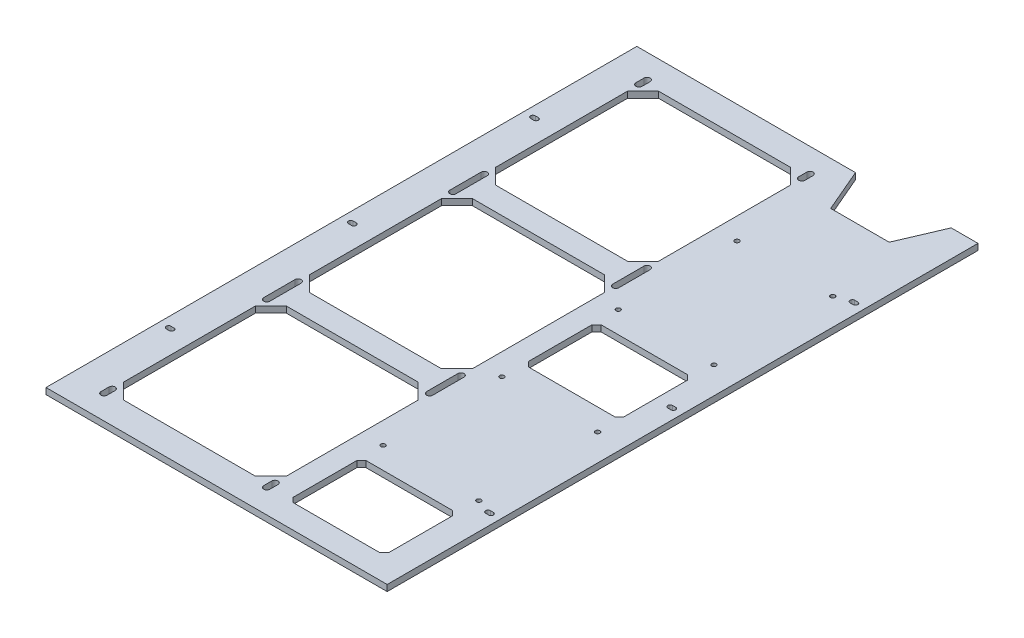
SolidWorks part; units mm, degrees
ref_plane "前基準面" through (0, 0, 0) normal (0, 0, 1) x (1, 0, 0)
ref_plane "上基準面" through (0, 0, 0) normal (0, 1, 0) x (1, 0, 0)
ref_plane "右基準面" through (0, 0, 0) normal (1, 0, 0) x (0, 0, -1)
ref_plane "平面1" through (0, 4, 0) normal (0, 1, 0) x (1, 0, 0)
sketch "草圖1" plane through (0, 4, 0) normal (0, 1, 0) x (1, 0, 0)
  line L0 (110, 190.5) -> (92.72, 190.5)
  line L1 (92.72, 190.5) -> (80.72, 162.5)
  line L2 (80.72, 162.5) -> (43, 162.5)
  line L3 (43, 162.5) -> (31, 190.5)
  line L4 (31, 190.5) -> (-110, 190.5)
  line L5 (-110, 190.5) -> (-110, -190.5)
  line L6 (-110, -190.5) -> (110, -190.5)
  line L7 (110, -190.5) -> (110, 190.5)
  line L8 (-104, 1.5) -> (-102, 1.5)
  line L9 (-102, -1.5) -> (-104, -1.5)
  line L10 (102, -116) -> (104, -116)
  line L11 (104, -119) -> (102, -119)
  line L12 (102, 1.5) -> (104, 1.5)
  line L13 (104, -1.5) -> (102, -1.5)
  line L14 (102, 119) -> (104, 119)
  line L15 (104, 116) -> (102, 116)
  line L16 (-104, -116) -> (-102, -116)
  line L17 (-102, -119) -> (-104, -119)
  line L18 (-104, 119) -> (-102, 119)
  line L19 (-102, 116) -> (-104, 116)
  line L20 (-90, -175.1) -> (-90, -169.9)
  line L21 (-86, -169.9) -> (-86, -175.1)
  line L22 (15, -70.1) -> (15, -49.9)
  line L23 (19, -49.9) -> (19, -70.1)
  line L24 (-90, -70.1) -> (-90, -49.9)
  line L25 (-86, -49.9) -> (-86, -70.1)
  line L26 (19, 175.1) -> (19, 169.9)
  line L27 (15, 169.9) -> (15, 175.1)
  line L28 (89.72, -23.5) -> (34, -23.5)
  line L29 (34, -23.5) -> (31, -20.5)
  line L30 (31, -20.5) -> (31, 20.5)
  line L31 (31, 20.5) -> (34, 23.5)
  line L32 (34, 23.5) -> (89.72, 23.5)
  line L33 (89.72, 23.5) -> (92.72, 20.5)
  line L34 (92.72, 20.5) -> (92.72, -20.5)
  line L35 (92.72, -20.5) -> (89.72, -23.5)
  line L36 (89.72, -175.1) -> (34, -175.1)
  line L37 (34, -175.1) -> (31, -172.1)
  line L38 (31, -172.1) -> (31, -131.1)
  line L39 (31, -131.1) -> (34, -128.1)
  line L40 (34, -128.1) -> (89.72, -128.1)
  line L41 (89.72, -128.1) -> (92.72, -131.1)
  line L42 (92.72, -131.1) -> (92.72, -172.1)
  line L43 (92.72, -172.1) -> (89.72, -175.1)
  line L44 (-78, -172.5) -> (-88, -162.5)
  line L45 (-88, -162.5) -> (-88, -77.5)
  line L46 (-88, -77.5) -> (-78, -67.5)
  line L47 (-78, -67.5) -> (7, -67.5)
  line L48 (7, -67.5) -> (17, -77.5)
  line L49 (17, -77.5) -> (17, -162.5)
  line L50 (17, -162.5) -> (7, -172.5)
  line L51 (7, -172.5) -> (-78, -172.5)
  line L52 (-78, -52.5) -> (-88, -42.5)
  line L53 (-88, -42.5) -> (-88, 42.5)
  line L54 (-88, 42.5) -> (-78, 52.5)
  line L55 (-78, 52.5) -> (7, 52.5)
  line L56 (7, 52.5) -> (17, 42.5)
  line L57 (17, 42.5) -> (17, -42.5)
  line L58 (17, -42.5) -> (7, -52.5)
  line L59 (7, -52.5) -> (-78, -52.5)
  line L60 (-86, 70.1) -> (-86, 49.9)
  line L61 (-90, 49.9) -> (-90, 70.1)
  line L62 (19, 70.1) -> (19, 49.9)
  line L63 (15, 49.9) -> (15, 70.1)
  line L64 (19, -169.9) -> (19, -175.1)
  line L65 (15, -175.1) -> (15, -169.9)
  line L66 (-86, 175.1) -> (-86, 169.9)
  line L67 (-90, 169.9) -> (-90, 175.1)
  line L68 (17, 162.5) -> (17, 77.5)
  line L69 (17, 77.5) -> (7, 67.5)
  line L70 (7, 67.5) -> (-78, 67.5)
  line L71 (-78, 67.5) -> (-88, 77.5)
  line L72 (-88, 77.5) -> (-88, 162.5)
  line L73 (-88, 162.5) -> (-78, 172.5)
  line L74 (-78, 172.5) -> (7, 172.5)
  line L75 (7, 172.5) -> (17, 162.5)
  arc A0 (-102, 1.5) -> (-102, -1.5) centre (-102, 0) cw
  arc A1 (-104, -1.5) -> (-104, 1.5) centre (-104, 0) cw
  arc A2 (104, -116) -> (104, -119) centre (104, -117.5) cw
  arc A3 (102, -119) -> (102, -116) centre (102, -117.5) cw
  arc A4 (104, 1.5) -> (104, -1.5) centre (104, 0) cw
  arc A5 (102, -1.5) -> (102, 1.5) centre (102, 0) cw
  arc A6 (104, 119) -> (104, 116) centre (104, 117.5) cw
  arc A7 (102, 116) -> (102, 119) centre (102, 117.5) cw
  arc A8 (-102, -116) -> (-102, -119) centre (-102, -117.5) cw
  arc A9 (-104, -119) -> (-104, -116) centre (-104, -117.5) cw
  arc A10 (-102, 119) -> (-102, 116) centre (-102, 117.5) cw
  arc A11 (-104, 116) -> (-104, 119) centre (-104, 117.5) cw
  circle A12 centre (31, 114.1) radius 1.45
  circle A13 centre (92.72, 114.1) radius 1.45
  circle A14 centre (31, 37.5) radius 1.45
  circle A15 centre (92.72, 37.5) radius 1.45
  circle A16 centre (31, -37.5) radius 1.45
  circle A17 centre (92.72, -37.5) radius 1.45
  circle A18 centre (31, -114.1) radius 1.45
  circle A19 centre (92.72, -114.1) radius 1.45
  arc A20 (-90, -169.9) -> (-86, -169.9) centre (-88, -169.9) cw
  arc A21 (-86, -175.1) -> (-90, -175.1) centre (-88, -175.1) cw
  arc A22 (15, -49.9) -> (19, -49.9) centre (17, -49.9) cw
  arc A23 (19, -70.1) -> (15, -70.1) centre (17, -70.1) cw
  arc A24 (-90, -49.9) -> (-86, -49.9) centre (-88, -49.9) cw
  arc A25 (-86, -70.1) -> (-90, -70.1) centre (-88, -70.1) cw
  arc A26 (19, 169.9) -> (15, 169.9) centre (17, 169.9) cw
  arc A27 (15, 175.1) -> (19, 175.1) centre (17, 175.1) cw
  arc A28 (-90, 70.1) -> (-86, 70.1) centre (-88, 70.1) cw
  arc A29 (-86, 49.9) -> (-90, 49.9) centre (-88, 49.9) cw
  arc A30 (15, 70.1) -> (19, 70.1) centre (17, 70.1) cw
  arc A31 (19, 49.9) -> (15, 49.9) centre (17, 49.9) cw
  arc A32 (15, -169.9) -> (19, -169.9) centre (17, -169.9) cw
  arc A33 (19, -175.1) -> (15, -175.1) centre (17, -175.1) cw
  arc A34 (-86, 169.9) -> (-90, 169.9) centre (-88, 169.9) cw
  arc A35 (-90, 175.1) -> (-86, 175.1) centre (-88, 175.1) cw
extrude "填料-伸長1" add sketch "草圖1" against normal blind 4
